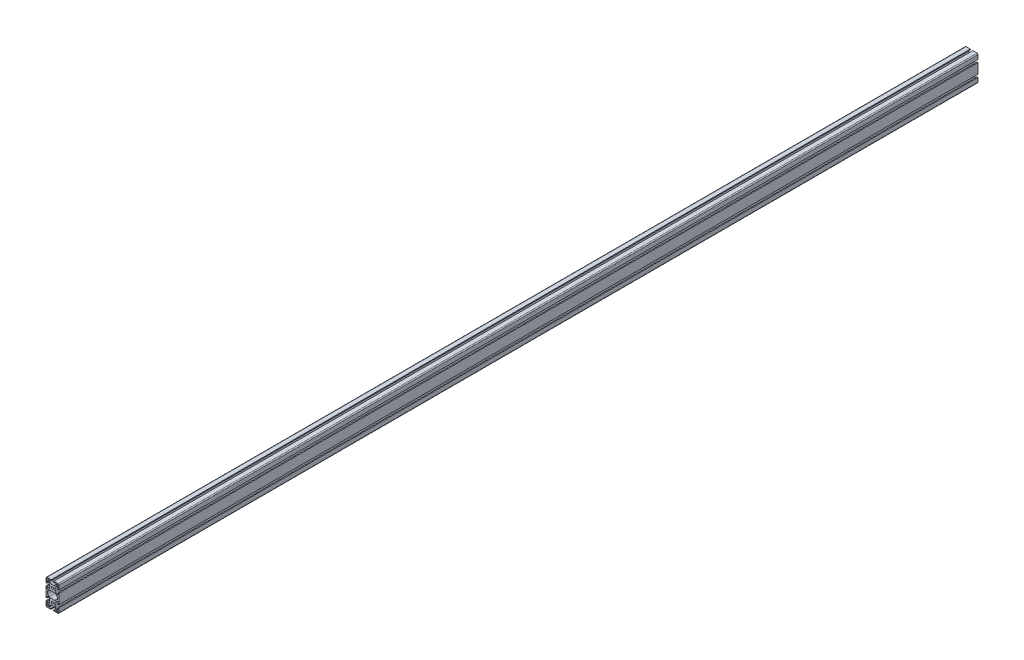
SolidWorks part; units mm, degrees
ref_plane "Front Plane" through (0, 0, 0) normal (0, 0, 1) x (1, 0, 0)
ref_plane "Top Plane" through (0, 0, 0) normal (0, 1, 0) x (1, 0, 0)
ref_plane "Right Plane" through (0, 0, 0) normal (1, 0, 0) x (0, 0, -1)
sketch "Sketch1" plane through (0, 0, -2897) normal (0, 0, 1) x (1, 0, 0)
  line L0 (-17, -40) -> (-4.1, -40)
  line L1 (-4.1, -40) -> (-4.1, -37)
  line L2 (-4.1, -37) -> (-10.5, -37)
  line L3 (-10.5, -37) -> (-10.5, -33.6627)
  line L4 (-10.0314, -32.5314) -> (-7.4645, -29.9645)
  line L5 (-3.9289, -28.5) -> (3.9289, -28.5)
  line L6 (7.4645, -29.9645) -> (10.0314, -32.5314)
  line L7 (10.5, -33.6627) -> (10.5, -37)
  line L8 (10.5, -37) -> (4.1, -37)
  line L9 (4.1, -37) -> (4.1, -40)
  line L10 (4.1, -40) -> (17, -40)
  line L11 (20, -37) -> (20, -24.1)
  line L12 (20, -24.1) -> (17, -24.1)
  line L13 (17, -24.1) -> (17, -30.5)
  line L14 (17, -30.5) -> (13.6627, -30.5)
  line L15 (12.5314, -30.0314) -> (9.9645, -27.4645)
  line L16 (8.5, -23.9289) -> (8.5, -16.0711)
  line L17 (9.9645, -12.5355) -> (12.5314, -9.9686)
  line L18 (13.6627, -9.5) -> (17, -9.5)
  line L19 (17, -9.5) -> (17, -15.9)
  line L20 (17, -15.9) -> (20, -15.9)
  line L21 (20, -15.9) -> (20, 15.9)
  line L22 (20, 15.9) -> (17, 15.9)
  line L23 (17, 15.9) -> (17, 9.5)
  line L24 (17, 9.5) -> (13.6627, 9.5)
  line L25 (12.5314, 9.9686) -> (9.9645, 12.5355)
  line L26 (8.5, 16.0711) -> (8.5, 23.9289)
  line L27 (9.9645, 27.4645) -> (12.5314, 30.0314)
  line L28 (13.6627, 30.5) -> (17, 30.5)
  line L29 (17, 30.5) -> (17, 24.1)
  line L30 (17, 24.1) -> (20, 24.1)
  line L31 (20, 24.1) -> (20, 37)
  line L32 (17, 40) -> (4.1, 40)
  line L33 (4.1, 40) -> (4.1, 37)
  line L34 (4.1, 37) -> (10.5, 37)
  line L35 (10.5, 37) -> (10.5, 33.6627)
  line L36 (10.0314, 32.5314) -> (7.4645, 29.9645)
  line L37 (3.9289, 28.5) -> (-3.9289, 28.5)
  line L38 (-7.4645, 29.9645) -> (-10.0314, 32.5314)
  line L39 (-10.5, 33.6627) -> (-10.5, 37)
  line L40 (-10.5, 37) -> (-4.1, 37)
  line L41 (-4.1, 37) -> (-4.1, 40)
  line L42 (-4.1, 40) -> (-17, 40)
  line L43 (-20, 37) -> (-20, 24.1)
  line L44 (-20, 24.1) -> (-17, 24.1)
  line L45 (-17, 24.1) -> (-17, 30.5)
  line L46 (-17, 30.5) -> (-13.6627, 30.5)
  line L47 (-12.5314, 30.0314) -> (-9.9645, 27.4645)
  line L48 (-8.5, 23.9289) -> (-8.5, 16.0711)
  line L49 (-9.9645, 12.5355) -> (-12.5314, 9.9686)
  line L50 (-13.6627, 9.5) -> (-17, 9.5)
  line L51 (-17, 9.5) -> (-17, 15.9)
  line L52 (-17, 15.9) -> (-20, 15.9)
  line L53 (-20, 15.9) -> (-20, -15.9)
  line L54 (-20, -15.9) -> (-17, -15.9)
  line L55 (-17, -15.9) -> (-17, -9.5)
  line L56 (-17, -9.5) -> (-13.6627, -9.5)
  line L57 (-12.5314, -9.9686) -> (-9.9645, -12.5355)
  line L58 (-8.5, -16.0711) -> (-8.5, -23.9289)
  line L59 (-9.9645, -27.4645) -> (-12.5314, -30.0314)
  line L60 (-13.6627, -30.5) -> (-17, -30.5)
  line L61 (-17, -30.5) -> (-17, -24.1)
  line L62 (-17, -24.1) -> (-20, -24.1)
  line L63 (-20, -24.1) -> (-20, -37)
  line L64 (-14.2426, -4.2426) -> (-9.9497, -8.5355)
  line L65 (-6.4142, -10) -> (6.4142, -10)
  line L66 (9.9497, -8.5355) -> (14.2426, -4.2426)
  line L67 (14.2426, 4.2426) -> (9.9497, 8.5355)
  line L68 (6.4142, 10) -> (-6.4142, 10)
  line L69 (-9.9497, 8.5355) -> (-14.2426, 4.2426)
  arc A0 (-20, -37) -> (-17, -40) centre (-17, -37) ccw
  arc A1 (-10.5, -33.6627) -> (-10.0314, -32.5314) centre (-8.9, -33.6627) cw
  arc A2 (-7.4645, -29.9645) -> (-3.9289, -28.5) centre (-3.9289, -33.5) cw
  arc A3 (3.9289, -28.5) -> (7.4645, -29.9645) centre (3.9289, -33.5) cw
  arc A4 (10.0314, -32.5314) -> (10.5, -33.6627) centre (8.9, -33.6627) cw
  arc A5 (17, -40) -> (20, -37) centre (17, -37) ccw
  arc A6 (13.6627, -30.5) -> (12.5314, -30.0314) centre (13.6627, -28.9) cw
  arc A7 (9.9645, -27.4645) -> (8.5, -23.9289) centre (13.5, -23.9289) cw
  arc A8 (8.5, -16.0711) -> (9.9645, -12.5355) centre (13.5, -16.0711) cw
  arc A9 (12.5314, -9.9686) -> (13.6627, -9.5) centre (13.6627, -11.1) cw
  arc A10 (13.6627, 9.5) -> (12.5314, 9.9686) centre (13.6627, 11.1) cw
  arc A11 (9.9645, 12.5355) -> (8.5, 16.0711) centre (13.5, 16.0711) cw
  arc A12 (8.5, 23.9289) -> (9.9645, 27.4645) centre (13.5, 23.9289) cw
  arc A13 (12.5314, 30.0314) -> (13.6627, 30.5) centre (13.6627, 28.9) cw
  arc A14 (20, 37) -> (17, 40) centre (17, 37) ccw
  arc A15 (10.5, 33.6627) -> (10.0314, 32.5314) centre (8.9, 33.6627) cw
  arc A16 (7.4645, 29.9645) -> (3.9289, 28.5) centre (3.9289, 33.5) cw
  arc A17 (-3.9289, 28.5) -> (-7.4645, 29.9645) centre (-3.9289, 33.5) cw
  arc A18 (-10.0314, 32.5314) -> (-10.5, 33.6627) centre (-8.9, 33.6627) cw
  arc A19 (-17, 40) -> (-20, 37) centre (-17, 37) ccw
  arc A20 (-13.6627, 30.5) -> (-12.5314, 30.0314) centre (-13.6627, 28.9) cw
  arc A21 (-9.9645, 27.4645) -> (-8.5, 23.9289) centre (-13.5, 23.9289) cw
  arc A22 (-8.5, 16.0711) -> (-9.9645, 12.5355) centre (-13.5, 16.0711) cw
  arc A23 (-12.5314, 9.9686) -> (-13.6627, 9.5) centre (-13.6627, 11.1) cw
  arc A24 (-13.6627, -9.5) -> (-12.5314, -9.9686) centre (-13.6627, -11.1) cw
  arc A25 (-9.9645, -12.5355) -> (-8.5, -16.0711) centre (-13.5, -16.0711) cw
  arc A26 (-8.5, -23.9289) -> (-9.9645, -27.4645) centre (-13.5, -23.9289) cw
  arc A27 (-12.5314, -30.0314) -> (-13.6627, -30.5) centre (-13.6627, -28.9) cw
  circle A28 centre (15, 35) radius 3
  circle A29 centre (15, -35) radius 3
  circle A30 centre (0, 20) radius 3.5
  circle A31 centre (0, -20) radius 3.5
  arc A32 (-14.2426, 4.2426) -> (-14.2426, -4.2426) centre (-10, 0) ccw
  arc A33 (-9.9497, -8.5355) -> (-6.4142, -10) centre (-6.4142, -5) ccw
  arc A34 (6.4142, -10) -> (9.9497, -8.5355) centre (6.4142, -5) ccw
  arc A35 (14.2426, -4.2426) -> (14.2426, 4.2426) centre (10, 0) ccw
  arc A36 (9.9497, 8.5355) -> (6.4142, 10) centre (6.4142, 5) ccw
  arc A37 (-6.4142, 10) -> (-9.9497, 8.5355) centre (-6.4142, 5) ccw
  circle A38 centre (-15, 35) radius 3
  circle A39 centre (-15, -35) radius 3
  dimension "D3" = 6
  dimension "D4" = 6
  dimension "D5" = 6
  dimension "D6" = 6
  dimension "D7" = 7
  dimension "D8" = 7
  dimension "D1" = 40
  dimension "D2" = 80
  dimension "D9" = 40
extrude "Boss-Extrude1" add sketch "Sketch1" along normal blind 2860
sketch "Sketch2" plane through (-8.5, 0, 0) normal (-1, 0, 0) x (0, 0, 1)
  line L1 (0, 0) -> (-40, 0)
  line L2 (0, 0) -> (0, 40)
  line L3 (0, 40) -> (-40, 40)
  line L4 (-40, 0) -> (-40, 40)
  line L5 (-2897, 40) -> (-2897, 37) construction
  line L6 (-2897, 40) -> (-2857, 40)
  line L7 (-2897, 40) -> (-2897, 0)
  line L8 (-2897, 0) -> (-2857, 0)
  line L9 (-2857, 40) -> (-2857, 0)
  line L10 (-37, 40) -> (-2897, 40) construction
extrude "Cut-Extrude1" [suppressed] cut sketch "Sketch2" against normal mid plane 80
equation "\"D4@Sketch1\"=\"D3@Sketch1\""
equation "\"D5@Sketch1\"=\"D3@Sketch1\""
equation "\"D6@Sketch1\"=\"D3@Sketch1\""
